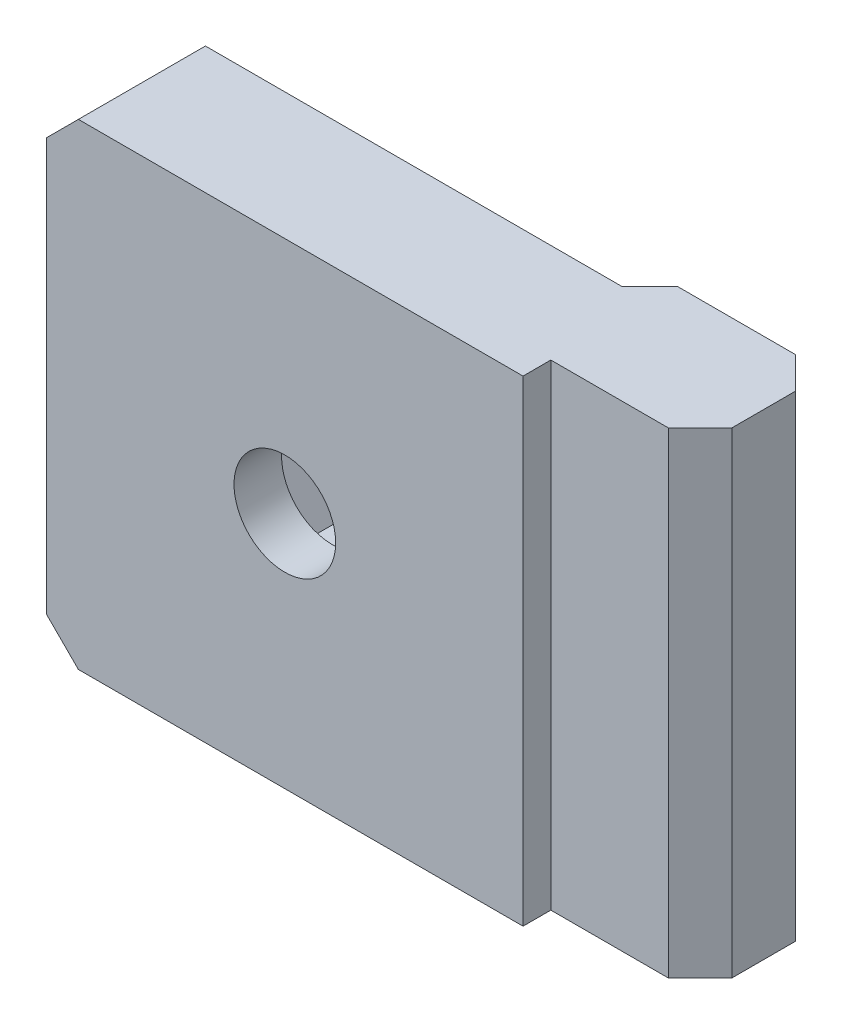
SolidWorks part; units mm, degrees
ref_plane "Alzado" through (0, 0, 0) normal (0, 0, 1) x (1, 0, 0)
ref_plane "Planta" through (0, 0, 0) normal (0, 1, 0) x (1, 0, 0)
ref_plane "Vista lateral" through (0, 0, 0) normal (1, 0, 0) x (0, 0, -1)
sketch "Croquis1" plane through (0, 0, 0) normal (0, 1, 0) x (1, 0, 0)
  line L0 (0, 0) -> (-30, 0)
  line L1 (-30, 0) -> (-30, 8)
  line L2 (-30, 8) -> (-1.75, 8)
  line L3 (-1.75, 8) -> (0, 9.75)
  line L4 (0, 9.75) -> (9.4, 9.75)
  line L5 (9.4, 9.75) -> (9.4, 1.75)
  line L6 (9.4, 1.75) -> (0, 1.75)
  line L7 (0, 1.75) -> (0, 0)
  line L8 (-15, 18.5318) -> (-15, -3.9407) construction
  point P10 (-30, 6.726)
  dimension "D1" = 1.75
  dimension "D2" = 30
  dimension "D3" = 8
  dimension "D4" = 9.4
  dimension "D5" = 15
  dimension "D6" = 45
extrude "Saliente-Extruir1" add sketch "Croquis1" along normal mid plane 30
sketch "Croquis2" plane through (0, 0, 0) normal (0, 0, 1) x (1, 0, 0)
  line L0 (0, 0) -> (-50000, 0) construction
  circle A0 centre (-15, 0) radius 3.2
  dimension "D2" = 6.4
  dimension "D1" = 15
extrude "Cortar-Extruir1" cut sketch "Croquis2" against normal through all
sketch "Croquis3" plane through (0, 0, 0) normal (0, 0, 1) x (1, 0, 0)
  line L1 (-9.2265, 0) -> (-12.1132, 5)
  line L2 (-12.1132, 5) -> (-17.8868, 5)
  line L3 (-17.8868, 5) -> (-20.7735, 0)
  line L4 (-20.7735, 0) -> (-17.8868, -5)
  line L5 (-17.8868, -5) -> (-12.1132, -5)
  line L6 (-12.1132, -5) -> (-9.2265, 0)
  circle A0 centre (-15, 0) radius 5 construction
  dimension "D1" = 10
extrude "Cortar-Extruir2" cut sketch "Croquis3" against normal through all from offset 3 offset against normal yes
chamfer "Chaflán1" distance 2 angle 45 4 edges at (9.4, 0, -1.75) (9.4, 0, -9.75) (-30, -15, -4) (-30, 15, -4)
